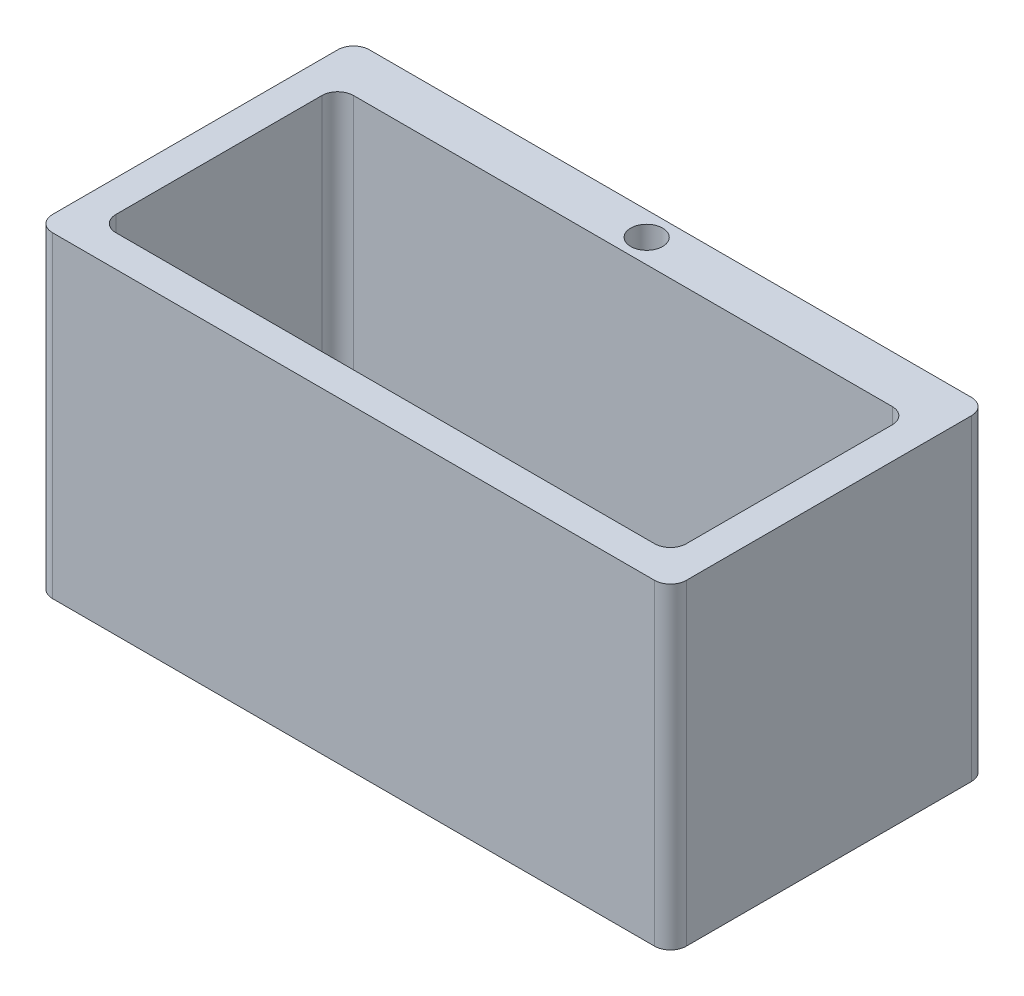
SolidWorks part; units mm, degrees
ref_plane "Front Plane" through (0, 0, 0) normal (0, 0, 1) x (1, 0, 0)
ref_plane "Top Plane" through (0, 0, 0) normal (0, 1, 0) x (1, 0, 0)
ref_plane "Right Plane" through (0, 0, 0) normal (1, 0, 0) x (0, 0, -1)
sketch "Sketch1" plane through (0, 0, 0) normal (0, 1, 0) x (1, 0, 0)
  line L1 (-133.7643, 68.0384) -> (348.8357, 68.0384)
  line L2 (-146.4643, 55.3384) -> (-146.4643, -173.2616)
  line L3 (-133.7643, -185.9616) -> (348.8357, -185.9616)
  line L4 (361.5357, 55.3384) -> (361.5357, -173.2616)
  circle A0 centre (107.5357, 48.9884) radius 12.8113
  circle A1 centre (107.5357, -69.4234) radius 19.6877
  arc A2 (-146.4643, -173.2616) -> (-133.7643, -185.9616) centre (-133.7643, -173.2616) ccw
  arc A3 (348.8357, -185.9616) -> (361.5357, -173.2616) centre (348.8357, -173.2616) ccw
  arc A4 (348.8357, 68.0384) -> (361.5357, 55.3384) centre (348.8357, 55.3384) cw
  arc A5 (-133.7643, 68.0384) -> (-146.4643, 55.3384) centre (-133.7643, 55.3384) ccw
  point P10 (-146.4643, -185.9616)
  point P15 (361.5357, 68.0384)
  point P18 (-146.4643, 68.0384)
  dimension "D3" = 12.7
  dimension "D1" = 508
  dimension "D2" = 254
  dimension "D4" = 254
  dimension "D5" = 254
  dimension "D6" = 19.05
extrude "Boss-Extrude1" add sketch "Sketch1" against normal blind 254
sketch "Sketch2" plane through (0, 0, 0) normal (0, 1, 0) x (1, 0, 0)
  line L0 (-146.4643, 55.3384) -> (-146.4643, -173.2616) construction
  line L1 (-108.3643, 29.9384) -> (323.4357, 29.9384)
  line L2 (-121.0643, 17.2384) -> (-121.0643, -147.8616)
  line L3 (-108.3643, -160.5616) -> (323.4357, -160.5616)
  line L4 (336.1357, 17.2384) -> (336.1357, -147.8616)
  line L5 (361.5357, -173.2616) -> (361.5357, 55.3384) construction
  line L6 (-133.7643, -185.9616) -> (348.8357, -185.9616) construction
  circle A1 centre (107.5357, 48.9884) radius 12.8113 construction
  arc A2 (323.4357, 29.9384) -> (336.1357, 17.2384) centre (323.4357, 17.2384) cw
  arc A3 (323.4357, -160.5616) -> (336.1357, -147.8616) centre (323.4357, -147.8616) ccw
  arc A4 (-121.0643, -147.8616) -> (-108.3643, -160.5616) centre (-108.3643, -147.8616) ccw
  arc A5 (-108.3643, 29.9384) -> (-121.0643, 17.2384) centre (-108.3643, 17.2384) ccw
  circle A6 centre (107.5357, -69.4234) radius 19.6877 construction
  dimension "D1" = 25.4
  dimension "D5" = 12.7
  dimension "D6" = 91.1383
  dimension "D2" = 25.4
  dimension "D3" = 25.4
  dimension "D4" = 19.05
extrude "Cut-Extrude1" cut sketch "Sketch2" against normal blind 241.3
